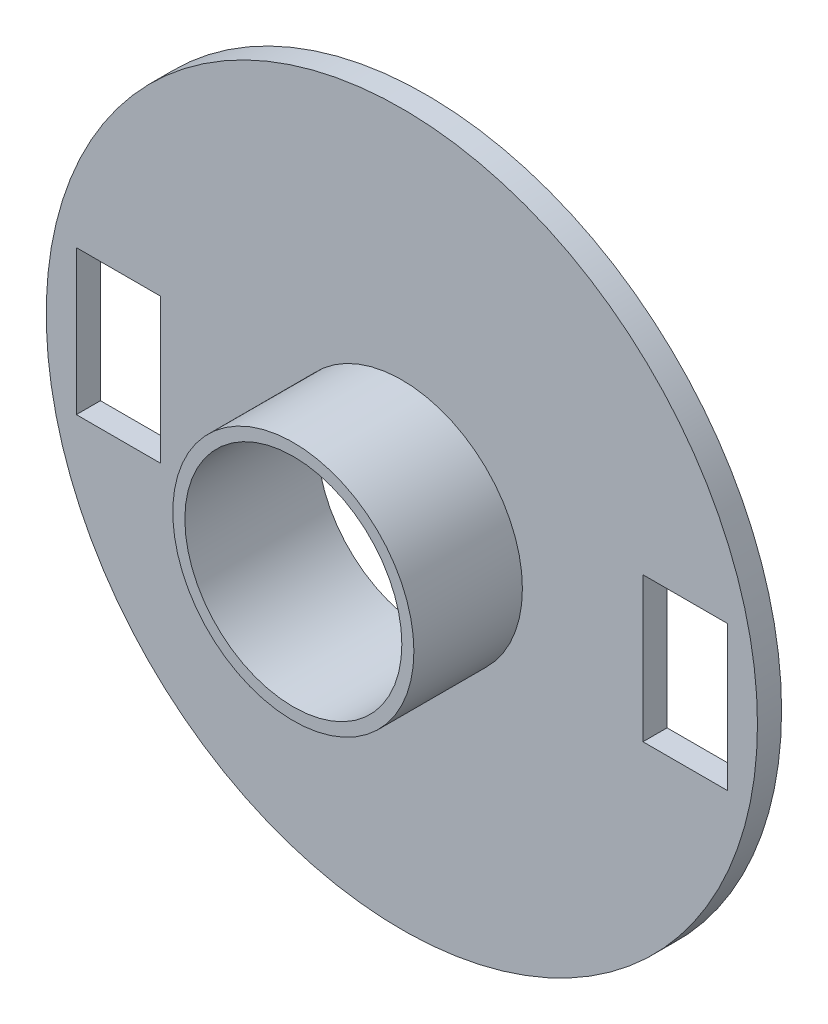
SolidWorks part; units mm, degrees
ref_plane "Front Plane" through (0, 0, 0) normal (0, 0, 1) x (1, 0, 0)
ref_plane "Top Plane" through (0, 0, 0) normal (0, 1, 0) x (1, 0, 0)
ref_plane "Right Plane" through (0, 0, 0) normal (1, 0, 0) x (0, 0, -1)
sketch "Sketch1" plane through (0, 0, 0) normal (0, 0, 1) x (1, 0, 0)
  circle A0 centre (0, 0) radius 14.75
  dimension "D1" = 29.5
extrude "Boss-Extrude1" add sketch "Sketch1" along normal blind 1
sketch "Sketch2" plane through (0, 0, 1) normal (0, 0, 1) x (1, 0, 0)
  circle A0 centre (0, 0) radius 5
  dimension "D1" = 10
extrude "Boss-Extrude2" add sketch "Sketch2" along normal blind 4.5
sketch "Sketch3" plane through (0, 0, 5.5) normal (0, 0, 1) x (1, 0, 0)
  line L0 (0, -0.2681) -> (0, -50000.2681) construction
  line L1 (-10, 3) -> (-13.5, 3)
  line L2 (-10, 3) -> (-10, -3)
  line L3 (-10, -3) -> (-13.5, -3)
  line L4 (-13.5, 3) -> (-13.5, -3)
  line L5 (-10, 3) -> (-13.5, -3) construction
  line L6 (-10, -3) -> (-13.5, 3) construction
  line L7 (0, 0) -> (-50000, 0) construction
  line L8 (10, 3) -> (10, -3)
  line L9 (10, -3) -> (13.5, -3)
  line L10 (13.5, 3) -> (13.5, -3)
  line L11 (10, 3) -> (13.5, 3)
  circle A0 centre (0, 0) radius 4.5
  point P3 (-11.75, 0)
  dimension "D1" = 9
  dimension "D2" = 10
  dimension "D3" = 3.5
  dimension "D4" = 6
extrude "Cut-Extrude1" cut sketch "Sketch3" against normal through all
